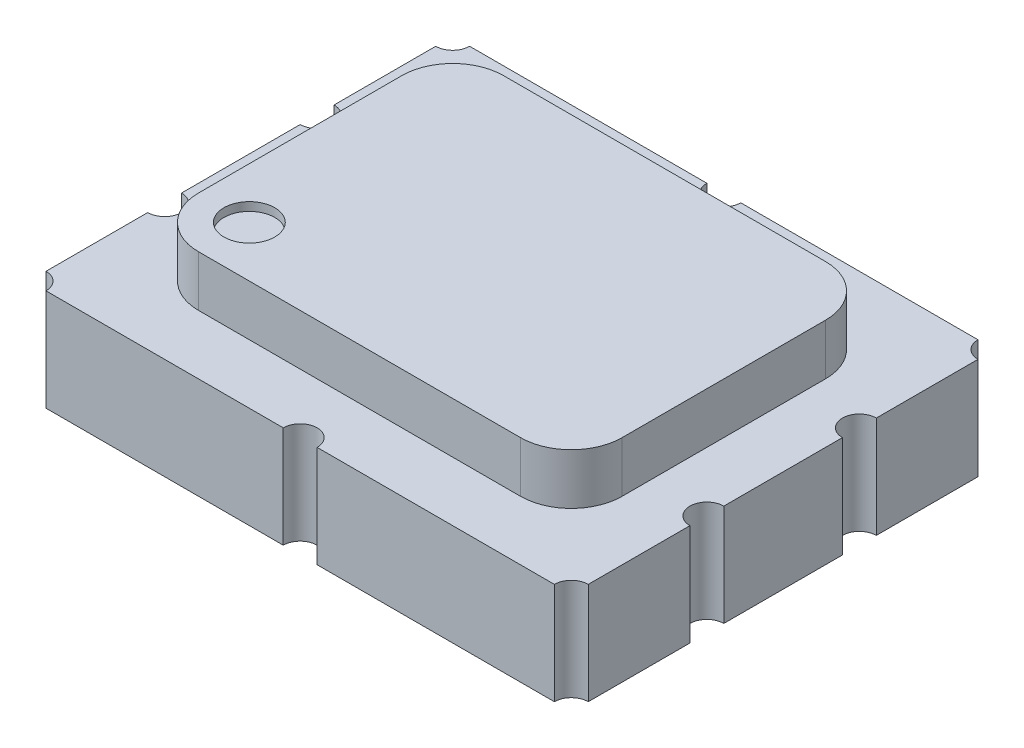
SolidWorks part; units mm, degrees
ref_plane "Front Plane" through (0, 0, 0) normal (0, 0, 1) x (1, 0, 0)
ref_plane "Top Plane" through (0, 0, 0) normal (0, 1, 0) x (1, 0, 0)
ref_plane "Right Plane" through (0, 0, 0) normal (1, 0, 0) x (0, 0, -1)
sketch "Sketch1" plane through (0, 0, 0) normal (0, 1, 0) x (1, 0, 0)
  line L1 (-1.6, 1.25) -> (1.6, 1.25)
  line L2 (-1.6, 1.25) -> (-1.6, -1.25)
  line L3 (-1.6, -1.25) -> (1.6, -1.25)
  line L4 (1.6, 1.25) -> (1.6, -1.25)
  line L5 (-1.6, 1.25) -> (1.6, -1.25) construction
  line L6 (-1.6, -1.25) -> (1.6, 1.25) construction
  point P0 (0, 0)
  dimension "D1" = 3.2
  dimension "D2" = 2.5
extrude "Boss-Extrude1" add sketch "Sketch1" along normal blind 0.6
sketch "Sketch2" plane through (0, 0.6, 0) normal (0, 1, 0) x (1, 0, 0)
  line L0 (1.6, -1.25) -> (1.6, 1.25) construction
  line L1 (-0.95, -0.9) -> (0.95, -0.9)
  line L2 (-1.25, -0.6) -> (-1.25, 0.6)
  line L3 (-0.95, 0.9) -> (0.95, 0.9)
  line L4 (1.25, -0.6) -> (1.25, 0.6)
  line L5 (-1.25, -0.9) -> (1.25, 0.9) construction
  line L6 (-1.25, 0.9) -> (1.25, -0.9) construction
  line L7 (1.6, 1.25) -> (-1.6, 1.25) construction
  arc A0 (0.95, -0.9) -> (1.25, -0.6) centre (0.95, -0.6) ccw
  arc A1 (0.95, 0.9) -> (1.25, 0.6) centre (0.95, 0.6) cw
  arc A2 (-0.95, -0.9) -> (-1.25, -0.6) centre (-0.95, -0.6) cw
  arc A3 (-1.25, 0.6) -> (-0.95, 0.9) centre (-0.95, 0.6) cw
  point P0 (0, 0)
  dimension "D3" = 0.3
  dimension "D1" = 0.35
  dimension "D2" = 0.35
extrude "Boss-Extrude2" add sketch "Sketch2" along normal blind 0.3
sketch "Sketch3" plane through (0, 0.6, 0) normal (0, 1, 0) x (1, 0, 0)
  line L0 (1.6, 1.25) -> (-1.6, 1.25) construction
  line L1 (-1.6, -1.25) -> (1.6, -1.25) construction
  line L2 (-1.6, 1.25) -> (-1.6, -1.25) construction
  line L3 (0, 0) -> (-1.6, 0) construction
  line L4 (0, 0) -> (0, 1.25) construction
  circle A0 centre (-1.6, 1.25) radius 0.1
  circle A1 centre (0, 1.25) radius 0.1
  circle A2 centre (1.6, 1.25) radius 0.1
  circle A3 centre (0, -1.25) radius 0.1
  circle A4 centre (-1.6, -1.25) radius 0.1
  circle A5 centre (1.6, -1.25) radius 0.1
  circle A6 centre (-1.6, 0.45) radius 0.1
  circle A7 centre (-1.6, -0.45) radius 0.1
  circle A8 centre (1.6, -0.45) radius 0.1
  circle A9 centre (1.6, 0.45) radius 0.1
  point P33 (0, 0)
  dimension "D1" = 0.2
  dimension "D2" = 0.9
extrude "Cut-Extrude1" cut sketch "Sketch3" against normal through all
sketch "Sketch4" plane through (0, 0.9, 0) normal (0, 1, 0) x (1, 0, 0)
  circle A0 centre (-0.95, -0.6) radius 0.15
  dimension "D1" = 0.3
extrude "Cut-Extrude2" cut sketch "Sketch4" against normal blind 0.05
